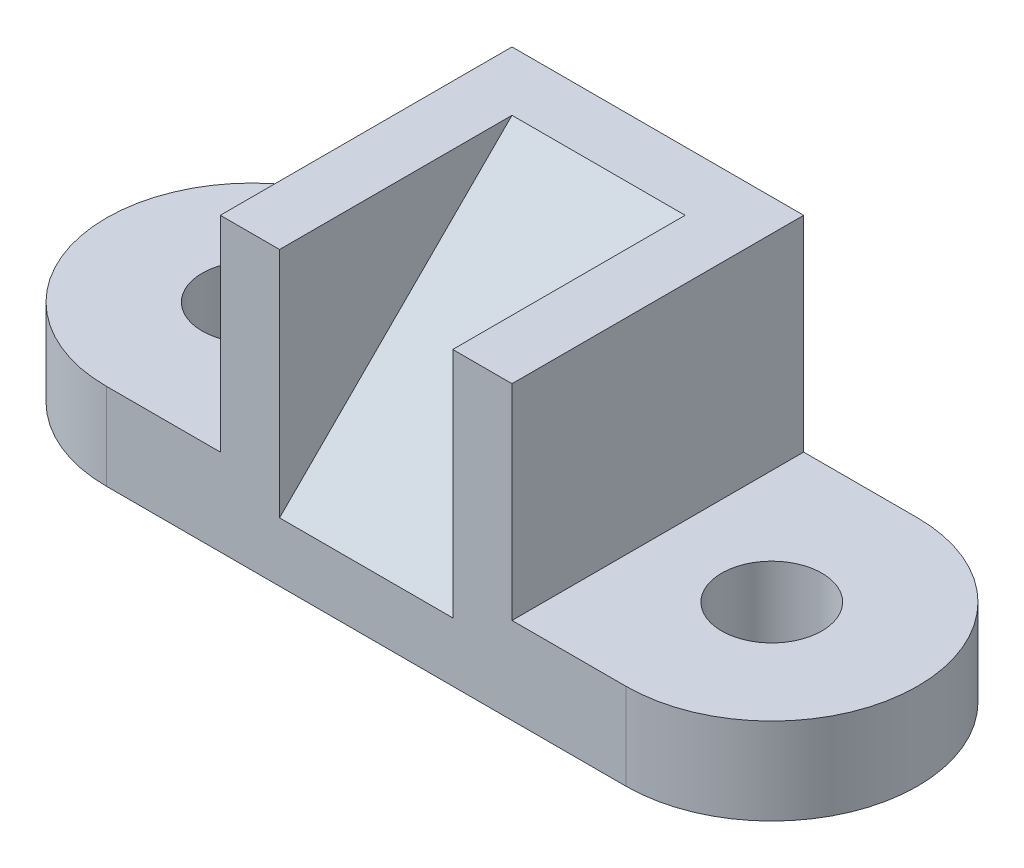
SolidWorks part; units mm, degrees
ref_plane "Front Plane" through (0, 0, 0) normal (0, 0, 1) x (1, 0, 0)
ref_plane "Top Plane" through (0, 0, 0) normal (0, 1, 0) x (1, 0, 0)
ref_plane "Right Plane" through (0, 0, 0) normal (1, 0, 0) x (0, 0, -1)
sketch "Sketch1" plane through (0, 0, 0) normal (0, 1, 0) x (1, 0, 0)
  line L0 (0, 0) -> (114, 0)
  line L5 (114, -64) -> (0, -64)
  line L8 (0, 29.0865) -> (0, -86.4174) construction
  line L9 (-67.2047, -32) -> (234.0653, -32) construction
  line L10 (114, 29.0865) -> (114, -87.8416) construction
  arc A4 (0, -64) -> (0, 0) centre (0, -32) cw
  circle A5 centre (0, -32) radius 11
  arc A6 (114, 0) -> (114, -64) centre (114, -32) cw
  circle A7 centre (114, -32) radius 11
  dimension "D1" = 114
  dimension "D2" = 32
  dimension "D4" = 22
  dimension "D3" = 22
extrude "Boss-Extrude1" add sketch "Sketch1" along normal blind 19
sketch "Sketch3" plane through (0, 19, 0) normal (0, 1, 0) x (1, 0, 0)
  line L0 (0, -64) -> (114, -64) construction
  line L1 (25, -64) -> (89, -64)
  line L2 (25, -64) -> (25, 0)
  line L3 (25, 0) -> (89, 0)
  line L4 (89, -64) -> (89, 0)
  line L5 (114, 0) -> (0, 0) construction
  line L6 (38, -64) -> (38, -13)
  line L7 (38, -13) -> (76, -13)
  line L8 (76, -13) -> (76, -64)
  circle A0 centre (0, -32) radius 11 construction
  dimension "D2" = 25
  dimension "D3" = 38
  dimension "D1" = 64
  dimension "D4" = 13
  dimension "D5" = 13
extrude "Boss-Extrude2" add sketch "Sketch3" along normal blind 45 contours L7 L8 L4 L0 L2 L6
sketch "Sketch7" plane through (0, 0, 64) normal (0, 0, 1) x (1, 0, 0)
  line L0 (38, 19) -> (76, 19)
  line L1 (38, 19) -> (38, 13)
  line L2 (76, 19) -> (76, 13)
  line L3 (38, 13) -> (76, 13)
  line L4 (0, 0) -> (114, 0) construction
  dimension "D1" = 13
extrude "Cut-Extrude8" cut sketch "Sketch7" against normal blind 51
sketch "Sketch8" plane through (38, 0, 0) normal (1, 0, 0) x (0, 0, -1)
  line L0 (-13, 64) -> (-64, 13)
  line L1 (-13, 64) -> (-13, 13)
  line L2 (-13, 13) -> (-64, 13)
extrude "Boss-Extrude3" add sketch "Sketch8" along normal blind 51
